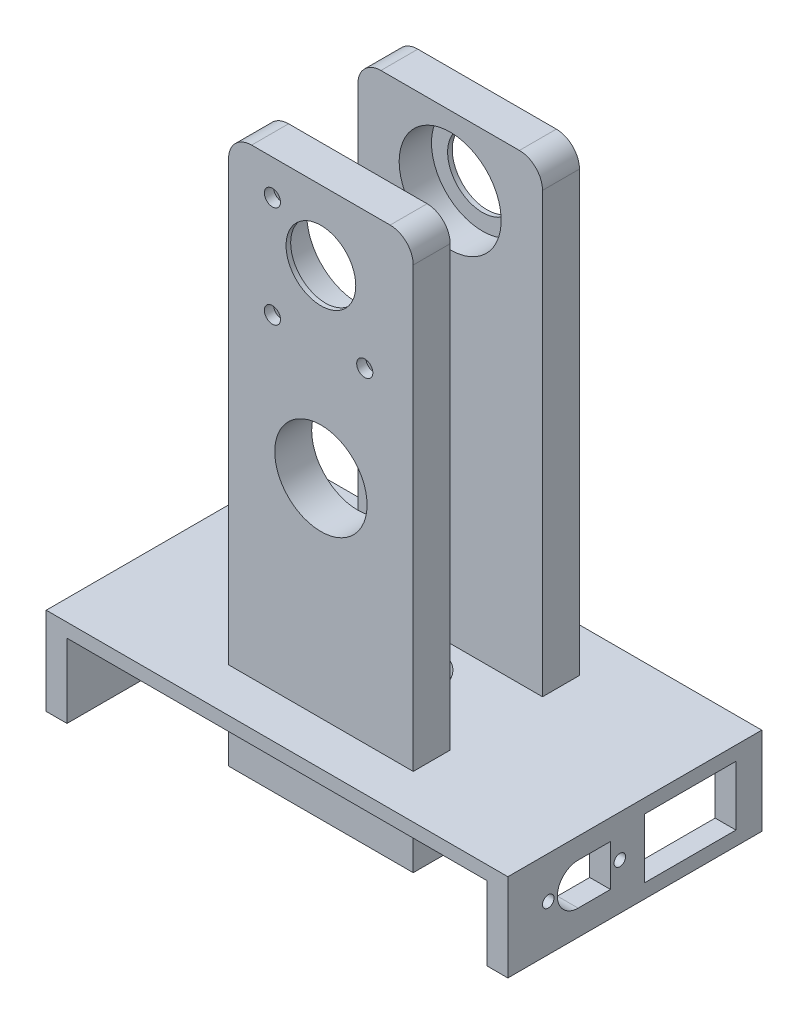
SolidWorks part; units mm, degrees
ref_plane "Front Plane" through (0, 0, 0) normal (0, 0, 1) x (1, 0, 0)
ref_plane "Top Plane" through (0, 0, 0) normal (0, 1, 0) x (1, 0, 0)
ref_plane "Right Plane" through (0, 0, 0) normal (1, 0, 0) x (0, 0, -1)
sketch "Sketch1" plane through (0, 0, 0) normal (0, 1, 0) x (1, 0, 0)
  line L1 (-50, -27.5) -> (50, -27.5)
  line L2 (-50, -27.5) -> (-50, 27.5)
  line L3 (-50, 27.5) -> (50, 27.5)
  line L4 (50, -27.5) -> (50, 27.5)
  line L5 (-50, -27.5) -> (50, 27.5) construction
  line L6 (-50, 27.5) -> (50, -27.5) construction
  point P0 (0, 0)
  dimension "D1" = 100
  dimension "D2" = 55
extrude "Boss-Extrude1" add sketch "Sketch1" along normal blind 19
sketch "Sketch2" plane through (0, 0, 0) normal (0, -1, 0) x (1, 0, 0)
  line L1 (-45.5, -45.5) -> (45.5, -45.5)
  line L2 (-45.5, -45.5) -> (-45.5, 45.5)
  line L3 (-45.5, 45.5) -> (45.5, 45.5)
  line L4 (45.5, -45.5) -> (45.5, 45.5)
  line L5 (-45.5, -45.5) -> (45.5, 45.5) construction
  line L6 (-45.5, 45.5) -> (45.5, -45.5) construction
  point P0 (0, 0)
  dimension "D1" = 91
  dimension "D2" = 91
extrude "Cut-Extrude1" cut sketch "Sketch2" against normal blind 16
sketch "Sketch3" plane through (50, 0, 0) normal (1, 0, 0) x (0, 0, -1)
  line L3 (-5.2727, 5.5) -> (-5.2727, 14.5)
  line L4 (-5.2727, 5.5) -> (-12.2784, 5.5)
  line L9 (-5.2727, 14.5) -> (-12.2784, 14.5)
  arc A1 (-12.2784, 5.5) -> (-12.2784, 14.5) centre (-12.2784, 10) cw
  circle A2 centre (-18.75, 10) radius 1.25
  circle A3 centre (-3.25, 10) radius 1.25
  point P17 (-11, 10)
extrude "Cut-Extrude3" cut sketch "Sketch3" against normal up to next
sketch "Sketch15" plane through (50, 0, 0) normal (1, 0, 0) x (0, 0, -1)
  line L0 (0, 0) -> (0, 19) construction
  line L1 (-27.5, 19) -> (27.5, 19) construction
  line L2 (0, 9.5) -> (12, 9.5) construction
  line L4 (2.1, 3.05) -> (21.9, 3.05)
  line L5 (2.1, 3.05) -> (2.1, 15.95)
  line L6 (2.1, 15.95) -> (21.9, 15.95)
  line L7 (21.9, 3.05) -> (21.9, 15.95)
  line L8 (2.1, 3.05) -> (21.9, 15.95) construction
  line L9 (2.1, 15.95) -> (21.9, 3.05) construction
  dimension "D1" = 12
  dimension "D2" = 19.8
  dimension "D3" = 12.9
extrude "Cut-Extrude13" cut sketch "Sketch15" against normal up to next
sketch "Sketch6" plane through (0, 19, 0) normal (0, 1, 0) x (1, 0, 0)
  line L0 (0, 0) -> (0, -10) construction
  line L1 (20, -10) -> (-20, -10)
  line L2 (-20, -10) -> (-20, -18)
  line L3 (20, -10) -> (20, -18)
  line L4 (20, -18) -> (-20, -18)
  point P6 (0, -10)
  dimension "D1" = 10
  dimension "D2" = 40
  dimension "D3" = 8
extrude "Boss-Extrude2" add sketch "Sketch6" along normal blind 100 and the other way blind 19
sketch "Sketch7" plane through (0, 0, 10) normal (0, 0, -1) x (-1, 0, 0)
  line L0 (0, 119) -> (0, 103.9) construction
  line L1 (-20, 119) -> (20, 119) construction
  circle A0 centre (0, 103.9) radius 11.05
  dimension "D2" = 22.1
  dimension "D1" = 15.1
extrude "Cut-Extrude5" cut sketch "Sketch7" against normal blind 7
sketch "Sketch8" plane through (0, 0, 18) normal (0, 0, 1) x (1, 0, 0)
  line L0 (0, 119) -> (0, 103.9) construction
  line L1 (-20, 119) -> (20, 119) construction
  circle A0 centre (0, 103.9) radius 7.55
  dimension "D2" = 15.1
  dimension "D1" = 15.1
extrude "Cut-Extrude6" cut sketch "Sketch8" against normal up to next (1 mm away)
fillet "Fillet1" radius 5 2 edges at (-20, 119, 14) (20, 119, 14)
mirror "Mirror2" about plane through (0, 0, 0) normal (0, 0, 1) of "Fillet1", "Cut-Extrude6", "Cut-Extrude5", "Boss-Extrude2"
sketch "Sketch9" plane through (0, 19, 0) normal (0, 1, 0) x (1, 0, 0)
  circle A0 centre (0, 0) radius 7.5
  dimension "D1" = 15
extrude "Cut-Extrude7" cut sketch "Sketch9" against normal up to next
sketch "Sketch12" plane through (0, 0, 18) normal (0, 0, 1) x (1, 0, 0)
  line L0 (0, 19) -> (0, 64) construction
  line L1 (-20, 19) -> (20, 19) construction
  circle A0 centre (0, 64) radius 10
  dimension "D2" = 20
  dimension "D1" = 45
extrude "Cut-Extrude10" cut sketch "Sketch12" against normal up to next
sketch "Sketch13" plane through (0, 0, 18) normal (0, 0, 1) x (1, 0, 0)
  line L0 (0, 103.9) -> (0, 86.9) construction
  line L1 (0, 86.9) -> (-13, 86.9) construction
  line L2 (-13, 86.9) -> (12, 86.9) construction
  line L3 (-13, 86.9) -> (-13, 113.9) construction
  line L4 (-13, 113.9) -> (12, 113.9) construction
  line L5 (12, 113.9) -> (12, 86.9) construction
  line L6 (-10.5, 86.9) -> (-10.5, 89.4) construction
  line L7 (-10.5, 89.4) -> (-13, 89.4) construction
  line L8 (-13, 100.4) -> (12, 100.4) construction
  line L9 (-0.5, 113.9) -> (-0.5, 86.9) construction
  circle A0 centre (-10.5, 89.4) radius 1.75
  circle A1 centre (-10.5, 111.4) radius 1.75
  circle A2 centre (9.5, 89.4) radius 1.75
  dimension "D7" = 3.5
  dimension "D1" = 17
  dimension "D2" = 13
  dimension "D3" = 27
  dimension "D4" = 25
  dimension "D5" = 2.5
  dimension "D6" = 2.5
extrude "Cut-Extrude11" cut sketch "Sketch13" against normal up to next
sketch "Sketch14" plane through (0, 0, 10) normal (0, 0, -1) x (-1, 0, 0)
  line L0 (10.5, 89.4) -> (-9.5, 89.4) construction
  line L1 (10.5, 89.4) -> (10.5, 111.4) construction
  line L2 (0.5, 89.4) -> (0.5, 91.4) construction
  line L3 (10.5, 100.4) -> (8.5, 100.4) construction
  line L4 (-11.1743, 92.3) -> (-7.8257, 92.3)
  line L5 (13.8486, 89.4) -> (12.1743, 92.3)
  line L6 (12.1743, 92.3) -> (8.8257, 92.3)
  line L7 (8.8257, 92.3) -> (7.1514, 89.4)
  line L8 (7.1514, 89.4) -> (8.8257, 86.5)
  line L9 (8.8257, 86.5) -> (12.1743, 86.5)
  line L10 (12.1743, 86.5) -> (13.8486, 89.4)
  line L11 (-12.8486, 89.4) -> (-11.1743, 92.3)
  line L12 (-11.1743, 86.5) -> (-12.8486, 89.4)
  line L13 (-7.8257, 86.5) -> (-11.1743, 86.5)
  line L14 (-6.1514, 89.4) -> (-7.8257, 86.5)
  line L15 (-7.8257, 92.3) -> (-6.1514, 89.4)
  line L16 (7.1514, 111.4) -> (8.8257, 114.3)
  line L17 (8.8257, 114.3) -> (12.1743, 114.3)
  line L18 (12.1743, 114.3) -> (13.8486, 111.4)
  line L19 (13.8486, 111.4) -> (12.1743, 108.5)
  line L20 (12.1743, 108.5) -> (8.8257, 108.5)
  line L21 (8.8257, 108.5) -> (7.1514, 111.4)
  circle A0 centre (10.5, 89.4) radius 2.9 construction
  dimension "D3" = 5.8
  dimension "D1" = 2
  dimension "D2" = 2
extrude "Cut-Extrude12" cut sketch "Sketch14" against normal blind 6
